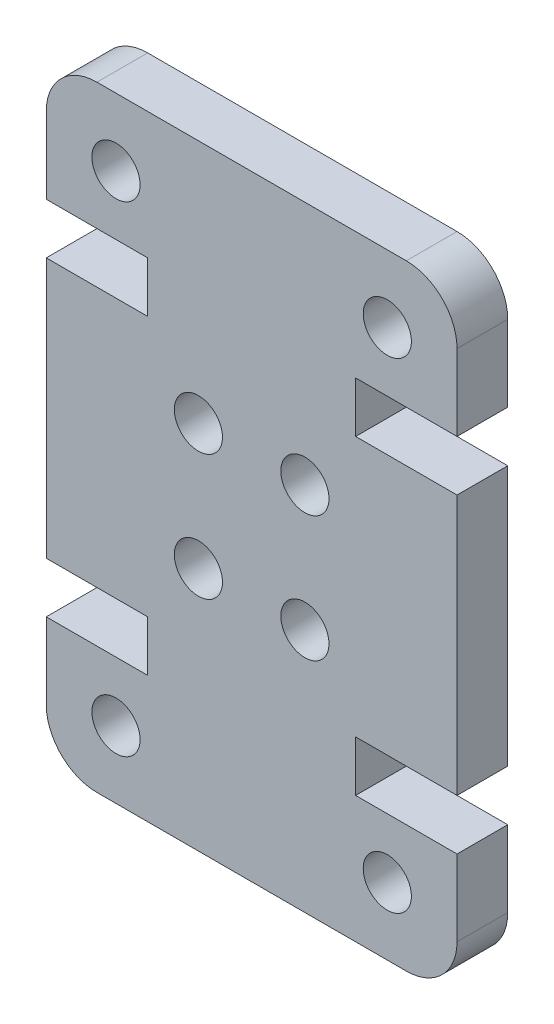
SolidWorks part; units mm, degrees
ref_plane "Front Plane" through (0, 0, 0) normal (0, 0, 1) x (1, 0, 0)
ref_plane "Top Plane" through (0, 0, 0) normal (0, 1, 0) x (1, 0, 0)
ref_plane "Right Plane" through (0, 0, 0) normal (1, 0, 0) x (0, 0, -1)
sketch "Sketch1" plane through (0, 0, 0) normal (0, 0, 1) x (1, 0, 0)
  line L0 (8.1, 24.26) -> (8.1, 0) construction
  line L1 (0, 12.13) -> (16.2, 12.13) construction
  line L2 (16.2, 17.26) -> (16.2, 7)
  line L3 (16.2, 2) -> (16.2, 5)
  line L4 (12.2, 5) -> (16.2, 5)
  line L5 (16.2, 7) -> (12.2, 7)
  line L6 (12.2, 7) -> (12.2, 5)
  line L7 (0, 22.26) -> (0, 19.26)
  line L8 (4, 19.26) -> (0, 19.26)
  line L9 (0, 17.26) -> (4, 17.26)
  line L10 (4, 17.26) -> (4, 19.26)
  line L11 (2, 24.26) -> (14.2, 24.26)
  line L12 (12.2, 17.26) -> (12.2, 19.26)
  line L13 (16.2, 17.26) -> (12.2, 17.26)
  line L14 (12.2, 19.26) -> (16.2, 19.26)
  line L15 (16.2, 22.26) -> (16.2, 19.26)
  line L21 (2, 0) -> (14.2, 0)
  line L25 (4, 7) -> (4, 5)
  line L28 (0, 7) -> (4, 7)
  line L30 (4, 5) -> (0, 5)
  line L34 (0, 2) -> (0, 5)
  line L38 (0, 17.26) -> (0, 7)
  circle A0 centre (13.45, 2.6536) radius 0.95
  circle A1 centre (10.2, 9.6536) radius 0.95
  arc A2 (16.2, 2) -> (14.2, 0) centre (14.2, 2) cw
  circle A3 centre (2.75, 21.6064) radius 0.95
  circle A4 centre (6, 14.6064) radius 0.95
  arc A5 (0, 22.26) -> (2, 24.26) centre (2, 22.26) cw
  arc A6 (16.2, 22.26) -> (14.2, 24.26) centre (14.2, 22.26) ccw
  circle A7 centre (10.2, 14.6064) radius 0.95
  circle A8 centre (13.45, 21.6064) radius 0.95
  arc A17 (0, 2) -> (2, 0) centre (2, 2) ccw
  circle A19 centre (6, 9.6536) radius 0.95
  circle A21 centre (2.75, 2.6536) radius 0.95
  point P16 (8.1, 12.13)
  dimension "D1" = 1.9
  dimension "D2" = 2
  dimension "D3" = 2.75
  dimension "D4" = 6
  dimension "D5" = 8.1
  dimension "D6" = 2.6536
  dimension "D7" = 5
  dimension "D9" = 9.6536
  dimension "D10" = 12.13
extrude "Boss-Extrude1" add sketch "Sketch1" along normal blind 2
equation "\"D5@Sketch1\"= \"fingerWidth@parametersSketch@prostheticParameters.SLDPRT\" / 2'PIP width"
equation "\"D10@Sketch1\"= ( \"HL@parametersSketch@prostheticParameters.SLDPRT\" * 0.196 - 4 - 8 ) / 2 'PIP length - Sil. Sht DIP - Sil. Sht PIP"
equation "\"D1@Sketch1\"= 1.5 + \"tol1@parametersSketch@prostheticParameters.SLDPRT\""
